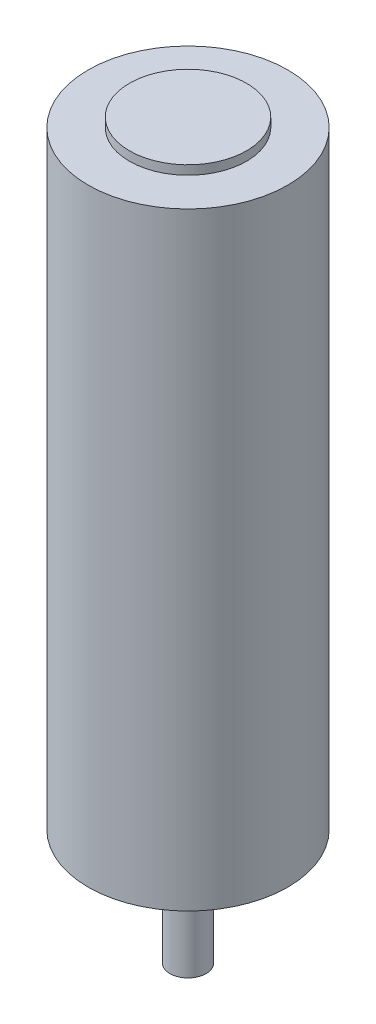
SolidWorks part; units mm, degrees
ref_plane "Front Plane" through (0, 0, 0) normal (0, 0, 1) x (1, 0, 0)
ref_plane "Top Plane" through (0, 0, 0) normal (0, 1, 0) x (1, 0, 0)
ref_plane "Right Plane" through (0, 0, 0) normal (1, 0, 0) x (0, 0, -1)
sketch "Sketch1" plane through (0, 0, 0) normal (0, 1, 0) x (1, 0, 0)
  circle A0 centre (0, 0) radius 11
  dimension "D1" = 22
extrude "Boss-Extrude1" add sketch "Sketch1" along normal mid plane 67
sketch "Sketch2" plane through (0, 33.5, 0) normal (0, 1, 0) x (1, 0, 0)
  circle A0 centre (0, 0) radius 6.45
  dimension "D1" = 12.9
extrude "Boss-Extrude2" add sketch "Sketch2" along normal blind 1
sketch "Sketch3" plane through (0, -33.5, 0) normal (0, -1, 0) x (1, 0, 0)
  circle A0 centre (0, 0) radius 6
  dimension "D1" = 12
extrude "Boss-Extrude3" add sketch "Sketch3" along normal blind 1
sketch "Sketch4" plane through (0, -34.5, 0) normal (0, -1, 0) x (1, 0, 0)
  circle A0 centre (0, 0) radius 3.25
  dimension "D1" = 6.5
extrude "Boss-Extrude4" add sketch "Sketch4" along normal blind 1.5
sketch "Sketch5" plane through (0, -36, 0) normal (0, -1, 0) x (-1, 0, 0)
  circle A0 centre (0, 0) radius 2
  dimension "D1" = 4
extrude "Boss-Extrude5" add sketch "Sketch5" along normal blind 10.25
sketch "Sketch9" plane through (0, -33.5, 0) normal (0, -1, 0) x (-1, 0, 0)
  point P0 (-7.25, 4.1856)
  point P2 (7.25, 4.1856)
  point P4 (0, -8.3717)
  point P7 (0, 0)
  point P9 (0, -8.1865)
  dimension "D1" = 14.5
  dimension "D2" = 14.5
  dimension "D3" = 14.5
  dimension "D4" = 8.3715
  dimension "D5" = 8.3717
hole_wizard "M3x0.5 Tapped Hole1" positions "Sketch9" profile "Sketch10" tap size "M3x0.5" standard "ANSI Metric"
sketch "Sketch10" plane through (7.25, -33.5, -4.1856) normal (1, 0, 0) x (0, 0, -1)
  line L0 (0, 0) -> (0, 7.7511)
  line L1 (0, 7.7511) -> (1.25, 7)
  line L2 (1.25, 7) -> (1.25, 0)
  line L5 (1.25, 0) -> (0, 0)
  line L10 (0, 7.7511) -> (-1.25, 7) construction
  line L11 (0, -6.35) -> (0, 107.95) construction
  dimension "Tap Drill Dia." = 2.5
  dimension "Tap Drill Depth" = 7
  dimension "Drill Angle" = 118
